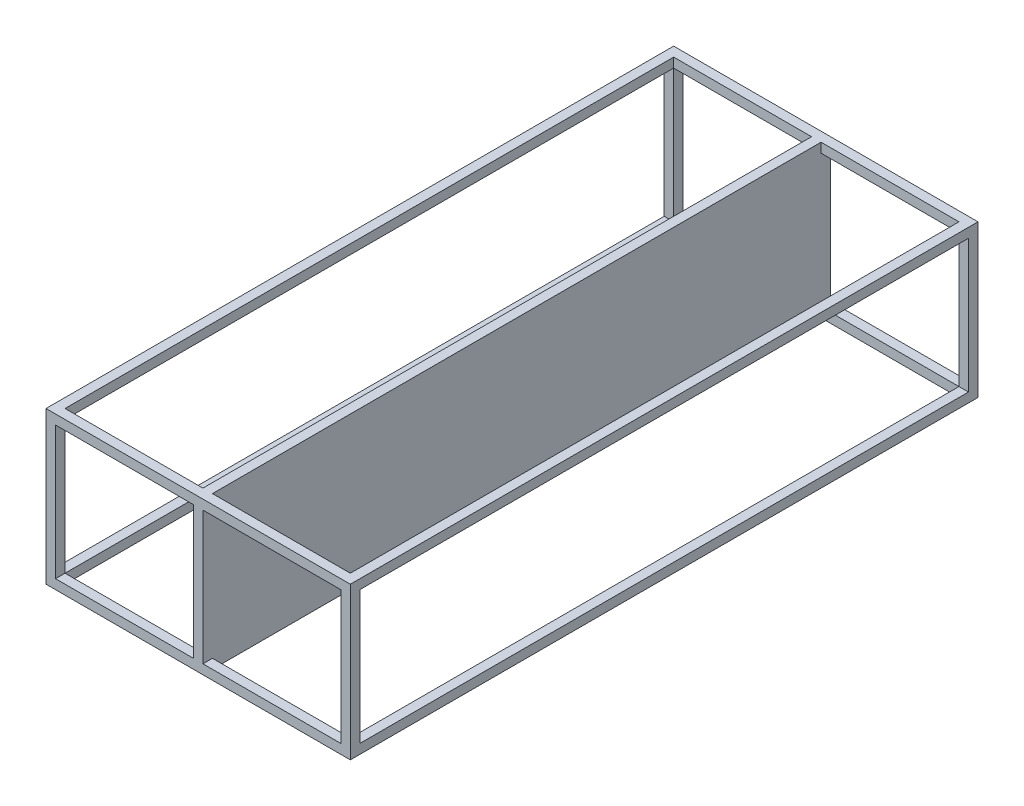
SolidWorks part; units mm, degrees
ref_plane "Front Plane" through (0, 0, 0) normal (0, 0, 1) x (1, 0, 0)
ref_plane "Top Plane" through (0, 0, 0) normal (0, 1, 0) x (1, 0, 0)
ref_plane "Right Plane" through (0, 0, 0) normal (1, 0, 0) x (0, 0, -1)
sketch "Sketch3" plane through (0, 0, 0) normal (0, 0, 1) x (1, 0, 0)
  line L0 (77.5, 41.6492) -> (5, 41.6492)
  line L1 (0, 0) -> (160, 0)
  line L2 (0, 0) -> (0, 80)
  line L3 (0, 80) -> (160, 80)
  line L4 (160, 0) -> (160, 80)
  line L5 (5, 75) -> (155, 75)
  line L6 (5, 75) -> (5, 5)
  line L7 (5, 5) -> (155, 5)
  line L8 (155, 75) -> (155, 5)
  line L9 (77.5, 75) -> (82.5, 75)
  line L10 (77.5, 75) -> (77.5, 5)
  line L11 (77.5, 5) -> (82.5, 5)
  line L12 (82.5, 75) -> (82.5, 5)
  line L13 (82.5, 41.6492) -> (155, 41.6492)
  dimension "D1" = 160
  dimension "D2" = 150
  dimension "D3" = 5
  dimension "D4" = 5
  dimension "D5" = 5
  dimension "D6" = 80
  dimension "D7" = 70
extrude "Boss-Extrude2" add sketch "Sketch3" along normal blind 5 contours L1 L4 L3 L2 L5 L8 L7 L6 | L12 L5 L10 L7
sketch "Sketch4" plane through (0, 0, 5) normal (0, 0, 1) x (1, 0, 0)
  line L13 (0, 0) -> (5, 0)
  line L14 (0, 0) -> (0, 5)
  line L15 (0, 5) -> (5, 5)
  line L16 (5, 0) -> (5, 5)
  line L17 (0, 80) -> (5, 80)
  line L18 (0, 80) -> (0, 75)
  line L19 (0, 75) -> (5, 75)
  line L20 (5, 80) -> (5, 75)
  line L21 (160, 80) -> (155, 80)
  line L22 (160, 80) -> (160, 75)
  line L23 (160, 75) -> (155, 75)
  line L24 (155, 80) -> (155, 75)
  line L25 (160, 0) -> (155, 0)
  line L26 (160, 0) -> (160, 5)
  line L27 (160, 5) -> (155, 5)
  line L28 (155, 0) -> (155, 5)
extrude "Boss-Extrude3" add sketch "Sketch4" along normal blind 320
ref_plane "Plane1" through (0, 0, 165) normal (0, 0, 1) x (1, 0, 0)
mirror "Mirror1" about plane through (0, 0, 165) normal (0, 0, 1) of "Boss-Extrude2"
sketch "Sketch5" plane through (0, 0, 5) normal (0, 0, 1) x (1, 0, 0)
  line L0 (5, 80) -> (155, 80) construction
  line L1 (77.5, 80) -> (82.5, 80)
  line L2 (77.5, 80) -> (77.5, 0)
  line L3 (77.5, 0) -> (82.5, 0)
  line L4 (82.5, 80) -> (82.5, 0)
  line L6 (77.5, 75) -> (77.5, 5) construction
  line L7 (82.5, 75) -> (82.5, 5) construction
  line L8 (5, 0) -> (155, 0) construction
extrude "Boss-Extrude4" add sketch "Sketch5" along normal up to next
